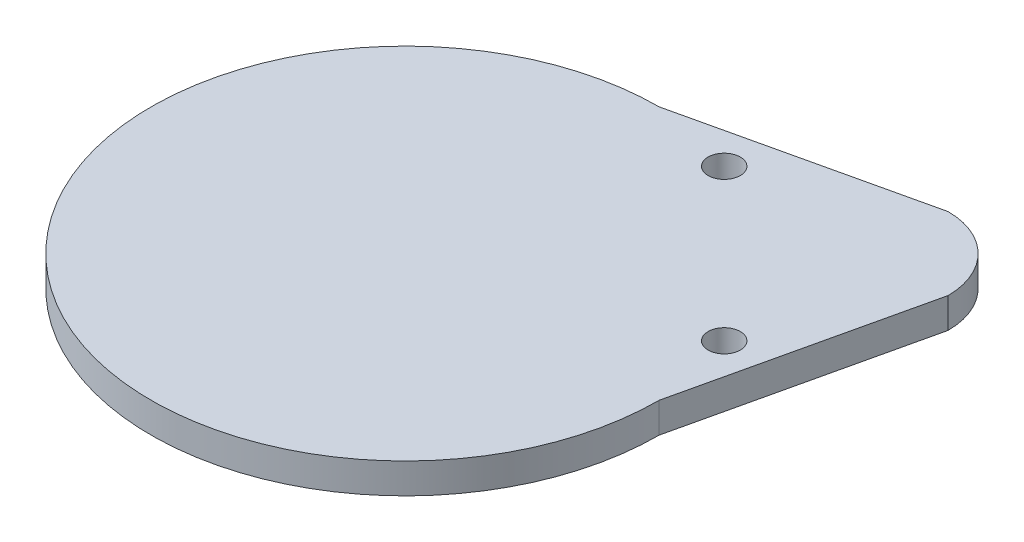
SolidWorks part; units mm, degrees
material "6061-T6 (SS)"
ref_plane "Front Plane" through (0, 0, 0) normal (0, 0, 1) x (1, 0, 0)
ref_plane "Top Plane" through (0, 0, 0) normal (0, 1, 0) x (1, 0, 0)
ref_plane "Right Plane" through (0, 0, 0) normal (1, 0, 0) x (0, 0, -1)
sketch "Sketch1" plane through (0, 0, 0) normal (0, 1, 0) x (1, 0, 0)
  line L0 (0, 0) -> (49.3914, 49.3914) construction
  line L1 (0, 53.3781) -> (49.3914, 64.6695)
  line L2 (53.3781, 0) -> (64.6695, 49.3914)
  circle A2 centre (0, 0) radius 53.3781 construction
  circle A3 centre (49.3914, 49.3914) radius 15.2781 construction
  arc A4 (49.3914, 64.6695) -> (64.6695, 49.3914) centre (49.3914, 49.3914) cw
  arc A5 (0, 53.3781) -> (53.3781, 0) centre (0, 0) ccw
  dimension "D1" = 53.3781
extrude "Boss-Extrude1" add sketch "Sketch1" along normal blind 6.35
sketch "Sketch3" plane through (0, 6.35, 0) normal (0, 1, 0) x (1, 0, 0)
  line L0 (0, 0) -> (49.3914, 49.3914) construction
  circle A0 centre (0, 0) radius 44.4881
  circle A1 centre (49.3914, 49.3914) radius 12.7381
  dimension "D1" = 88.9762
  dimension "D2" = 25.4762
extrude "Cut-Extrude1" cut sketch "Sketch3" against normal through all
sketch "Sketch8" [suppressed] plane through (0, 0, 0) normal (0, -1, 0) x (1, 0, 0)
  line L0 (0, 0) -> (49.3914, -49.3914) construction
  circle A0 centre (0, 0) radius 50.8381
  circle A1 centre (49.3914, -49.3914) radius 12.7381
  dimension "D1" = 101.6762
  dimension "D2" = 25.4762
extrude "Cut-Extrude2" [suppressed] cut sketch "Sketch8" against normal blind 3.175
hole_wizard "1/4 Clearance Hole1" positions "Sketch10" profile "Sketch9" hole size "1/4" standard "Ansi Inch"
sketch "Sketch10" plane through (0, 0, 0) normal (0, -1, 0) x (1, 0, 0)
  line L2 (49.3914, -49.3914) -> (49.3914, -17.6414) construction
  line L4 (49.3914, -49.3914) -> (17.6414, -49.3914) construction
  point P0 (49.3914, -17.6414)
  point P19 (17.6414, -49.3914)
  dimension "D1" = 31.75
  dimension "D2" = 31.75
sketch "Sketch9" plane through (49.3914, 0, -17.6414) normal (1, 0, 0) x (0, 0, -1)
  line L0 (0, 0) -> (0, 27.4298)
  line L1 (0, 27.4298) -> (3.3782, 25.4)
  line L2 (3.3782, 25.4) -> (3.3782, 0)
  line L5 (3.3782, 0) -> (0, 0)
  line L10 (0, 27.4298) -> (-3.3782, 25.4) construction
  line L11 (0, -6.35) -> (0, 107.95) construction
  dimension "Hole Dia." = 6.7564
  dimension "Hole Depth" = 25.4
  dimension "Drill Angle" = 118
sketch "Sketch11" plane through (0, 6.35, 0) normal (0, 1, 0) x (-1, 0, 0)
  circle A0 centre (0, 0) radius 44.4881
extrude "Boss-Extrude3" add sketch "Sketch11" against normal blind 3.175
sketch "Sketch12" plane through (0, 6.35, 0) normal (0, 1, 0) x (-1, 0, 0)
  circle A0 centre (-49.3914, -49.3914) radius 12.7381
extrude "Boss-Extrude4" add sketch "Sketch12" against normal blind 3.175
